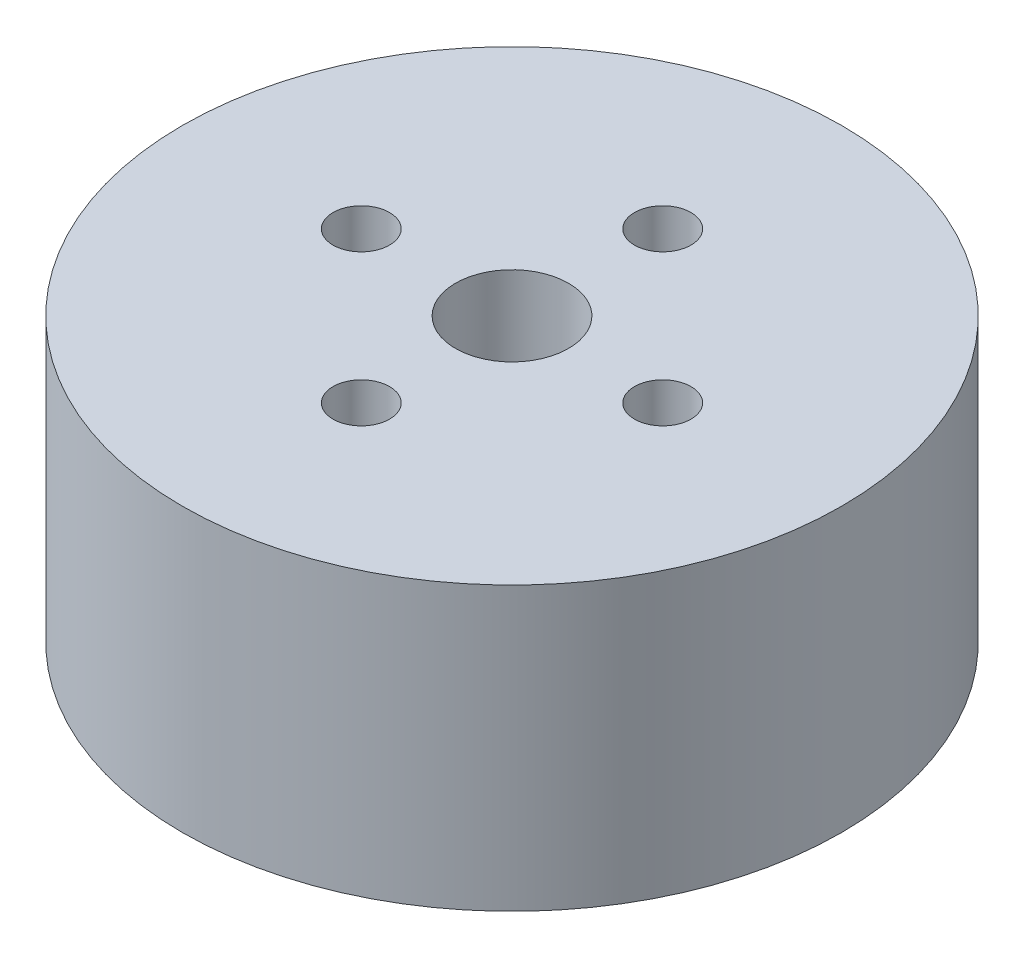
SolidWorks part; units mm, degrees
ref_plane "前视基准面" through (0, 0, 0) normal (0, 0, 1) x (1, 0, 0)
ref_plane "上视基准面" through (0, 0, 0) normal (0, 1, 0) x (1, 0, 0)
ref_plane "右视基准面" through (0, 0, 0) normal (1, 0, 0) x (0, 0, -1)
sketch "草图1" plane through (0, 0, 0) normal (0, 1, 0) x (1, 0, 0)
  circle A0 centre (0, 0) radius 17.5
  dimension "D1" = 35
extrude "凸台-拉伸1" add sketch "草图1" along normal blind 15
sketch "草图2" plane through (0, 0, 0) normal (0, -1, 0) x (-1, 0, 0)
  circle A0 centre (0, 0) radius 3
  dimension "D1" = 6
extrude "切除-拉伸1" cut sketch "草图2" against normal through all
sketch "草图3" plane through (0, 15, 0) normal (0, 1, 0) x (1, 0, 0)
  circle A0 centre (0, 8) radius 1.5
  circle A1 centre (8, 0) radius 1.5
  circle A2 centre (0, -8) radius 1.5
  circle A3 centre (-8, 0) radius 1.5
  dimension "D1" = 8
  dimension "D2" = 8
  dimension "D3" = 3
  dimension "D4" = 8
  dimension "D5" = 8
  dimension "D6" = 3
  dimension "D7" = 3
  dimension "D8" = 3
  dimension "D9" = 8
  dimension "D10" = 8
  dimension "D11" = 8
extrude "切除-拉伸2" cut sketch "草图3" against normal blind 5
sketch "草图4" plane through (0, 0, 0) normal (0, -1, 0) x (1, 0, 0)
  circle A0 centre (0, 9.5) radius 1.5
  circle A1 centre (9.5, 0) radius 1.5
  circle A2 centre (0, -9.5) radius 1.5
  circle A3 centre (-9.5, 0) radius 1.5
  circle A4 centre (0, 0) radius 3 construction
  dimension "D1" = 3
  dimension "D2" = 9.5
  dimension "D3" = 3
  dimension "D4" = 9.5
  dimension "D5" = 3
  dimension "D6" = 9.5
  dimension "D7" = 3
  dimension "D8" = 9.5
extrude "切除-拉伸3" cut sketch "草图4" against normal blind 5
